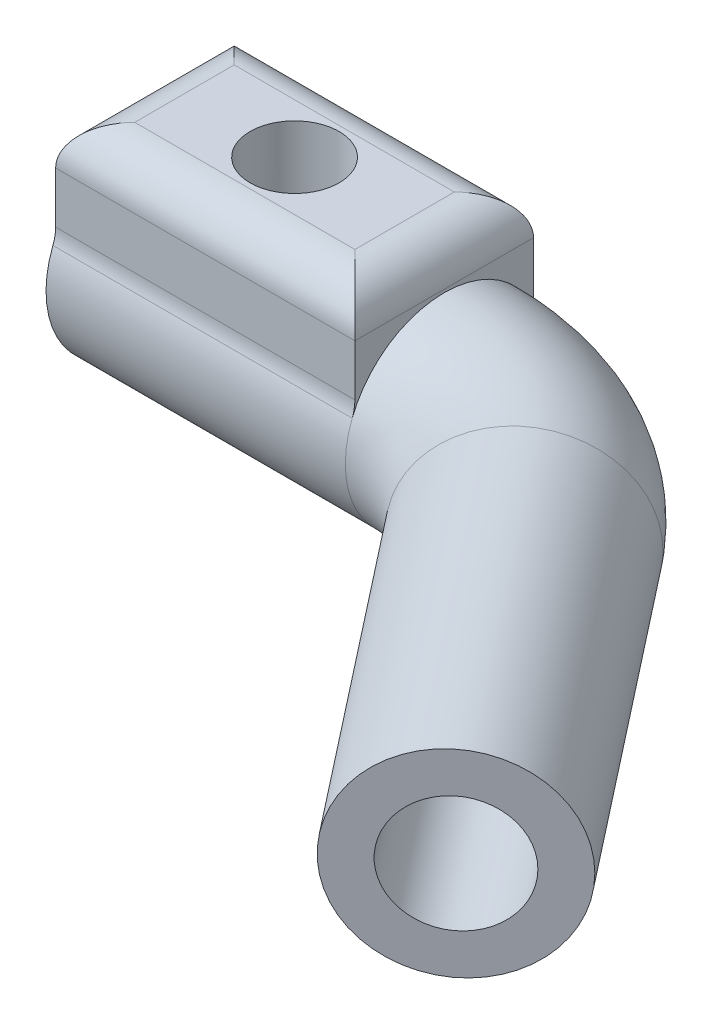
SolidWorks part; units mm, degrees
ref_plane "Front" through (0, 0, 0) normal (0, 0, 1) x (1, 0, 0)
ref_plane "Top" through (0, 0, 0) normal (0, 1, 0) x (1, 0, 0)
ref_plane "Right" through (0, 0, 0) normal (1, 0, 0) x (0, 0, -1)
sketch "Sketch1" plane through (0, 0, 0) normal (0, 1, 0) x (1, 0, 0)
  line L0 (0, 0) -> (15.1284, 0)
  line L1 (23.0028, -3.8361) -> (35.4097, -19.6861)
  line L2 (15.1284, 0) -> (20, 0) construction
  line L3 (23.0028, -3.8361) -> (20, 0) construction
  arc A0 (23.0028, -3.8361) -> (15.1284, 0) centre (15.1284, -10) ccw
  point P10 (20, 0)
  dimension "D1" = 10
  dimension "D2" = 128.053
  dimension "D3" = 20
  dimension "D4" = 25
sketch "Sketch2" plane through (0, 0, 0) normal (1, 0, 0) x (0, 0, -1)
  circle A1 centre (0, 0) radius 5
  dimension "D1" = 10
sweep "Sweep1" add profiles "Sketch2" path "Sketch1"
sketch "Sketch3" plane through (0, 0, 0) normal (0, 1, 0) x (1, 0, 0)
  line L1 (0, 0) -> (6.25, 0) construction
  line L2 (0, -5) -> (15.1284, -5) construction
  line L3 (12.5, 5) -> (0, 5)
  line L4 (12.5, 5) -> (12.5, -5)
  line L5 (12.5, -5) -> (0, -5)
  line L6 (0, 5) -> (0, -5)
  line L7 (12.5, 5) -> (0, -5) construction
  line L8 (12.5, -5) -> (0, 5) construction
  line L9 (0, 5) -> (0, -5) construction
  dimension "D1" = 12.5
extrude "Boss-Extrude1" [suppressed] add sketch "Sketch3" along normal blind 5
sketch "Sketch4" plane through (0, 0, 0) normal (-1, 0, 0) x (0, 0, 1)
  line L0 (-2.1633, 2.15) -> (2.1633, 2.15)
  circle A0 centre (0, 0) radius 3.05 construction
  arc A1 (-2.1633, 2.15) -> (2.1633, 2.15) centre (0, 0) ccw
  point P5 (0, -3.05)
  dimension "D1" = 6.1
  dimension "D2" = 5.2
extrude "Cut-Extrude1" cut sketch "Sketch4" against normal blind 12.5
sketch "Sketch5" plane through (23.0084, 0, 29.3935) normal (0.6164, 0, 0.7874) x (0.7874, 0, -0.6164)
  circle A0 centre (15.7489, 0) radius 2.95
  dimension "D1" = 5.9
sketch "Sketch6" [suppressed] plane through (0, 5, 0) normal (0, 1, 0) x (1, 0, 0)
  line L0 (0, 5) -> (12.5, -5) construction
  line L1 (0, -5) -> (12.5, 5) construction
  circle A0 centre (6.25, 0) radius 1.7
  point P8 (6.25, 0)
  dimension "D1" = 3.4
extrude "Cut-Extrude2" [suppressed] cut sketch "Sketch6" against normal up to next
extrude "Cut-Extrude3" cut sketch "Sketch5" against normal blind 10
fillet "Fillet1" [suppressed] radius 1
sketch "Sketch14" plane through (0, 2.15, 0) normal (0, -1, 0) x (1, 0, 0)
  line L6 (0, 5) -> (15.1284, 5)
  line L7 (0, 5) -> (0, -5)
  line L8 (0, -5) -> (15.1284, -5)
  line L9 (15.1284, 5) -> (15.1284, -5)
extrude "Cut-Extrude4" cut sketch "Sketch14" against normal blind 5
sketch "Sketch15" plane through (0, 2.15, 0) normal (0, 1, 0) x (1, 0, 0)
  line L1 (0, 4.5141) -> (15.1284, 4.5141)
  line L2 (0, 4.5141) -> (0, -4.5141)
  line L3 (0, -4.5141) -> (15.1284, -4.5141)
  line L4 (15.1284, 4.5141) -> (15.1284, -4.5141)
extrude "Boss-Extrude3" add sketch "Sketch15" along normal blind 5
fillet "Fillet2" radius 2 2 edges at (7.5642, 2.15, -4.5141) (7.5642, 2.15, 4.5141)
fillet "Fillet3" radius 2 4 edges at (7.5642, 7.15, -4.5141) (15.1284, 7.15, 0) (7.5642, 7.15, 4.5141) (0, 7.15, 0)
sketch "Sketch16" plane through (0, 7.15, 0) normal (0, 1, 0) x (1, 0, 0)
  line L0 (2, 2.5141) -> (13.1284, -2.5141) construction
  line L1 (2, -2.5141) -> (13.1284, 2.5141) construction
  line L2 (13.1284, 2.5141) -> (2, 2.5141) construction
  circle A0 centre (7.5642, 0) radius 2.25
  dimension "D1" = 4.5
extrude "Cut-Extrude5" cut sketch "Sketch16" against normal up to next
